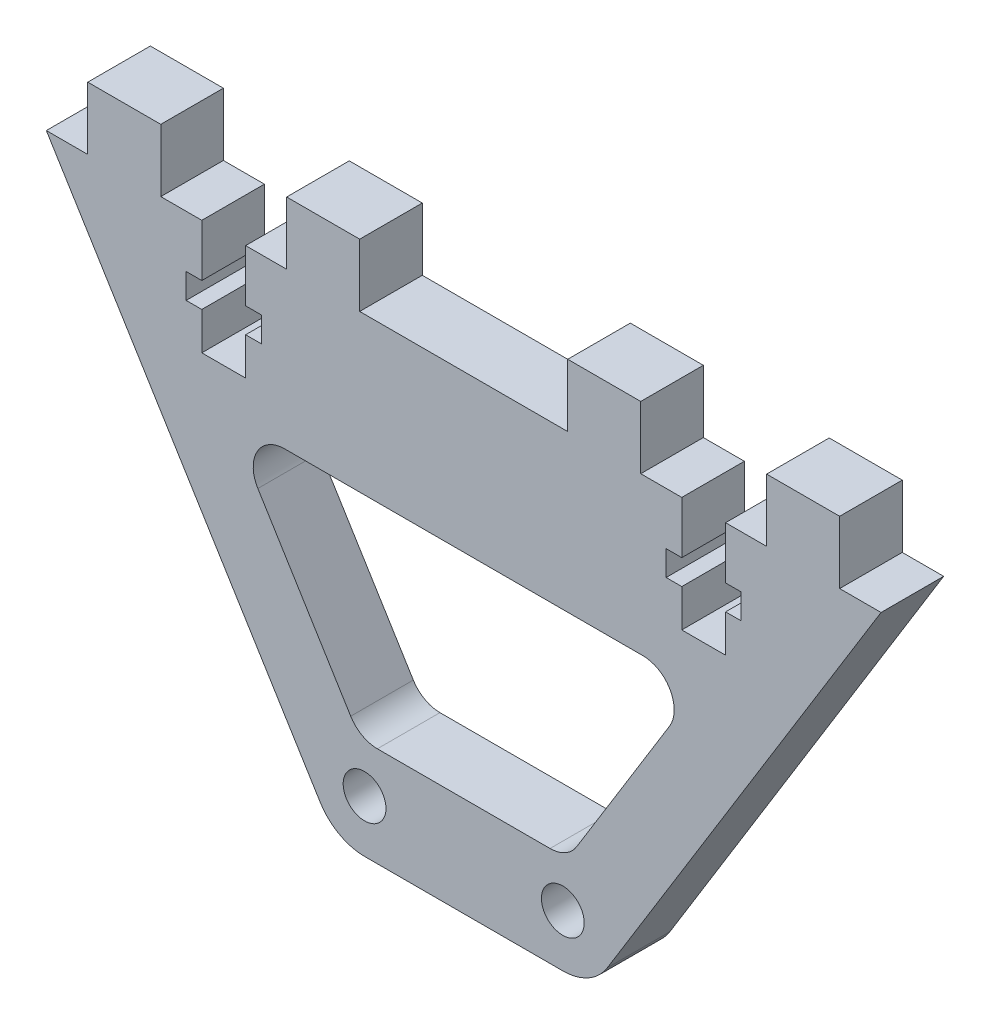
SolidWorks part; units mm, degrees
material "Клен"
ref_plane "Спереди" through (0, 0, 0) normal (0, 0, 1) x (1, 0, 0)
ref_plane "Сверху" through (0, 0, 0) normal (0, 1, 0) x (1, 0, 0)
ref_plane "Справа" through (0, 0, 0) normal (1, 0, 0) x (0, 0, -1)
sketch "Эскиз1" plane through (0, 0, 0) normal (0, 0, 1) x (1, 0, 0)
  line L0 (-40, 0) -> (40, 0)
  line L2 (0, -62.2549) -> (0, 44.8529) construction
  line L4 (-9.5, -45) -> (9.5, -45)
  line L5 (-13.7577, -42.6215) -> (-40, 0)
  line L6 (13.7577, -42.6215) -> (40, 0)
  line L7 (-17.1738, -15) -> (17.1738, -15)
  line L8 (19.7284, -19.5729) -> (10.8298, -34.0256)
  line L9 (8.2752, -35.4527) -> (-8.2752, -35.4527)
  line L10 (-10.8298, -34.0256) -> (-19.7284, -19.5729)
  arc A0 (9.5, -45) -> (13.7577, -42.6215) centre (9.5, -40) ccw
  arc A1 (-9.5, -45) -> (-13.7577, -42.6215) centre (-9.5, -40) cw
  circle A2 centre (-9.5, -40) radius 2.05
  circle A3 centre (9.5, -40) radius 2.05
  arc A4 (10.8298, -34.0256) -> (8.2752, -35.4527) centre (8.2752, -32.4527) cw
  arc A5 (-8.2752, -35.4527) -> (-10.8298, -34.0256) centre (-8.2752, -32.4527) cw
  arc A6 (17.1738, -15) -> (19.7284, -19.5729) centre (17.1738, -18) cw
  arc A7 (-17.1738, -15) -> (-19.7284, -19.5729) centre (-17.1738, -18) ccw
  point P7 (0, 0)
  point P9 (0, -45)
  point P13 (12.2932, -45)
  point P16 (-12.2932, -45)
  dimension "D3" = 5
  dimension "D4" = 4.1
  dimension "D9" = 3
  dimension "D2" = 80
  dimension "D5" = 9.5
  dimension "D6" = 45
  dimension "D1" = 15
  dimension "D7" = 7
  dimension "D8" = 7
extrude "Бобышка-Вытянуть1" add sketch "Эскиз1" along normal blind 6
ref_plane "Плоскость1" through (0, 0, 0) normal (1, 0, 0) x (0, 0, -1)
sketch "Эскиз2" plane through (-23, -50, 0) normal (0, 0, -1) x (-1, 0, 0)
  line L1 (-13.0318, 50) -> (-6.0318, 50)
  line L2 (-13.0318, 50) -> (-13.0318, 56)
  line L3 (-13.0318, 56) -> (-6.0318, 56)
  line L4 (-6.0318, 50) -> (-6.0318, 56)
  line L5 (13, 56) -> (-13, 56) construction
  line L6 (0, 53.4074) -> (0, -162.0434) construction
  line L7 (13.0318, 50) -> (6.0318, 50)
  line L8 (6.0318, 50) -> (6.0318, 56)
  line L9 (13.0318, 56) -> (6.0318, 56)
  line L10 (13.0318, 50) -> (13.0318, 56)
  dimension "D1" = 7
extrude "Бобышка-Вытянуть2" add sketch "Эскиз2" against normal blind 6
sketch "Эскиз3" plane through (-23, -50, 0) normal (0, 0, -1) x (-1, 0, 0)
  line L3 (-2.1, 45) -> (-3.6, 45)
  line L4 (-3.6, 45) -> (-3.6, 42.6)
  line L5 (-3.6, 42.6) -> (-2.1, 42.6)
  line L8 (0, 53.4074) -> (0, -162.0434) construction
  line L11 (3.6, 42.6) -> (2.1, 42.6)
  line L12 (3.6, 45) -> (3.6, 42.6)
  line L13 (2.1, 45) -> (3.6, 45)
  line L16 (-2.1, 45) -> (-2.1, 50)
  line L17 (-2.1, 50) -> (2.1, 50)
  line L18 (2.1, 50) -> (2.1, 45)
  line L19 (2.1, 42.6) -> (2.1, 39)
  line L20 (2.1, 39) -> (-2.1, 39)
  line L21 (-2.1, 39) -> (-2.1, 42.6)
  point P15 (0, 43.65)
  point P20 (0, 50)
  dimension "D2" = 7.2
  dimension "D3" = 2.4
  dimension "D4" = 4.2
extrude "Вырез-Вытянуть1" cut sketch "Эскиз3" against normal through all
other "Авто-элемент1<DIN967-3>"
sketch "Эскиз21" plane through (-23, -50, 6) normal (0, 0, 1) x (1, 0, 0)
  line L1 (-13.0318, 50) -> (-6.0318, 50)
  line L2 (-13.0318, 50) -> (-13.0318, 56)
  line L3 (-13.0318, 56) -> (-6.0318, 56)
  line L4 (-6.0318, 50) -> (-6.0318, 56)
  line L5 (13, 56) -> (-13, 56) construction
  line L6 (0, 53.4074) -> (0, -162.0434) construction
  line L7 (13.0318, 50) -> (6.0318, 50)
  line L8 (6.0318, 50) -> (6.0318, 56)
  line L9 (13.0318, 56) -> (6.0318, 56)
  line L10 (13.0318, 50) -> (13.0318, 56)
  dimension "D1" = 7
extrude "Бобышка-Вытянуть21" add sketch "Эскиз21" against normal blind 6
other "Авто-элемент2<DIN967-4>"
sketch "Эскиз22" plane through (23, -50, 0) normal (0, 0, -1) x (-1, 0, 0)
  line L1 (-13.0318, 50) -> (-6.0318, 50)
  line L2 (-13.0318, 50) -> (-13.0318, 56)
  line L3 (-13.0318, 56) -> (-6.0318, 56)
  line L4 (-6.0318, 50) -> (-6.0318, 56)
  line L5 (13, 56) -> (-13, 56) construction
  line L6 (0, 53.4074) -> (0, -162.0434) construction
  line L7 (13.0318, 50) -> (6.0318, 50)
  line L8 (6.0318, 50) -> (6.0318, 56)
  line L9 (13.0318, 56) -> (6.0318, 56)
  line L10 (13.0318, 50) -> (13.0318, 56)
  dimension "D1" = 7
extrude "Бобышка-Вытянуть22" add sketch "Эскиз22" against normal blind 6
sketch "Эскиз32" plane through (23, -50, 0) normal (0, 0, -1) x (-1, 0, 0)
  line L3 (-2.1, 45) -> (-3.6, 45)
  line L4 (-3.6, 45) -> (-3.6, 42.6)
  line L5 (-3.6, 42.6) -> (-2.1, 42.6)
  line L8 (0, 53.4074) -> (0, -162.0434) construction
  line L11 (3.6, 42.6) -> (2.1, 42.6)
  line L12 (3.6, 45) -> (3.6, 42.6)
  line L13 (2.1, 45) -> (3.6, 45)
  line L16 (-2.1, 45) -> (-2.1, 50)
  line L17 (-2.1, 50) -> (2.1, 50)
  line L18 (2.1, 50) -> (2.1, 45)
  line L19 (2.1, 42.6) -> (2.1, 39)
  line L20 (2.1, 39) -> (-2.1, 39)
  line L21 (-2.1, 39) -> (-2.1, 42.6)
  point P15 (0, 43.65)
  point P20 (0, 50)
  dimension "D2" = 7.2
  dimension "D3" = 2.4
  dimension "D4" = 4.2
extrude "Вырез-Вытянуть12" cut sketch "Эскиз32" against normal through all
other "Авто-элемент3<DIN967-5>"
other "Авто-элемент4<DIN967-6>"
equation "\"D8@Эскиз1\"=\"D7@Эскиз1\""
